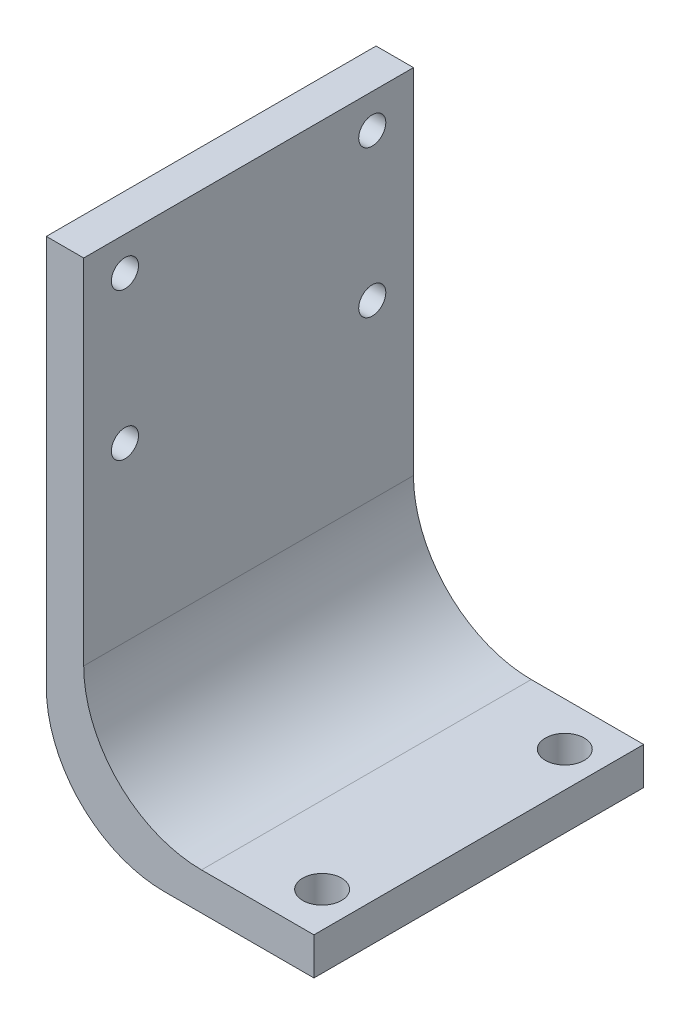
SolidWorks part; units mm, degrees
ref_plane "Front Plane" through (0, 0, 0) normal (0, 0, 1) x (1, 0, 0)
ref_plane "Top Plane" through (0, 0, 0) normal (0, 1, 0) x (1, 0, 0)
ref_plane "Right Plane" through (0, 0, 0) normal (1, 0, 0) x (0, 0, -1)
sketch "Sketch1" plane through (0, 0, 0) normal (0, 1, 0) x (1, 0, 0)
  line L1 (-11.3614, 14) -> (11.3614, 14)
  line L2 (-11.3614, 14) -> (-11.3614, -14)
  line L3 (-11.3614, -14) -> (11.3614, -14)
  line L4 (11.3614, 14) -> (11.3614, -14)
  line L5 (-11.3614, 14) -> (11.3614, -14) construction
  line L6 (-11.3614, -14) -> (11.3614, 14) construction
  circle A0 centre (8.3614, 10.3033) radius 1.65
  circle A1 centre (8.3614, -10.3033) radius 1.65
  point P0 (0, 0)
  dimension "D1" = 3.3
  dimension "D2" = 28
  dimension "D3" = 3
extrude "Boss-Extrude1" add sketch "Sketch1" along normal blind 3.175
sketch "Sketch2" plane through (0, 3.175, 0) normal (0, 1, 0) x (1, 0, 0)
  line L0 (-11.3614, -14) -> (11.3614, -14) construction
  line L1 (-11.3614, 14) -> (-8.1864, 14)
  line L2 (-11.3614, 14) -> (-11.3614, -14)
  line L3 (-11.3614, -14) -> (-8.1864, -14)
  line L4 (-8.1864, 14) -> (-8.1864, -14)
  dimension "D1" = 3.175
extrude "Boss-Extrude2" add sketch "Sketch2" along normal blind 40
fillet "Fillet1" radius 10 2 edges at (-11.3614, 0, 0) (-8.1864, 3.175, 0)
sketch "Sketch3" plane through (-11.3614, 0, 0) normal (-1, 0, 0) x (0, 0, 1)
  line L0 (0, 43.175) -> (0, 13.175) construction
  line L1 (14, 43.175) -> (-14, 43.175) construction
  line L2 (14, 13.175) -> (-14, 13.175) construction
  line L4 (10.5, 40.3058) -> (-10.5, 40.3058) construction
  line L5 (10.5, 40.3058) -> (10.5, 27.8058) construction
  line L6 (10.5, 27.8058) -> (-10.5, 27.8058) construction
  line L7 (-10.5, 40.3058) -> (-10.5, 27.8058) construction
  line L8 (10.5, 40.3058) -> (-10.5, 27.8058) construction
  line L9 (10.5, 27.8058) -> (-10.5, 40.3058) construction
  circle A0 centre (10.5, 40.3058) radius 1.15
  circle A1 centre (10.5, 27.8058) radius 1.15
  circle A2 centre (-10.5, 40.3058) radius 1.15
  circle A3 centre (-10.5, 27.8058) radius 1.15
  point P6 (0, 34.0558)
  dimension "D3" = 2.3
  dimension "D1" = 21
  dimension "D2" = 12.5
extrude "Cut-Extrude1" cut sketch "Sketch3" against normal up to surface (3.175 mm away) up to face at (-8.1864, 28.175, 0)
